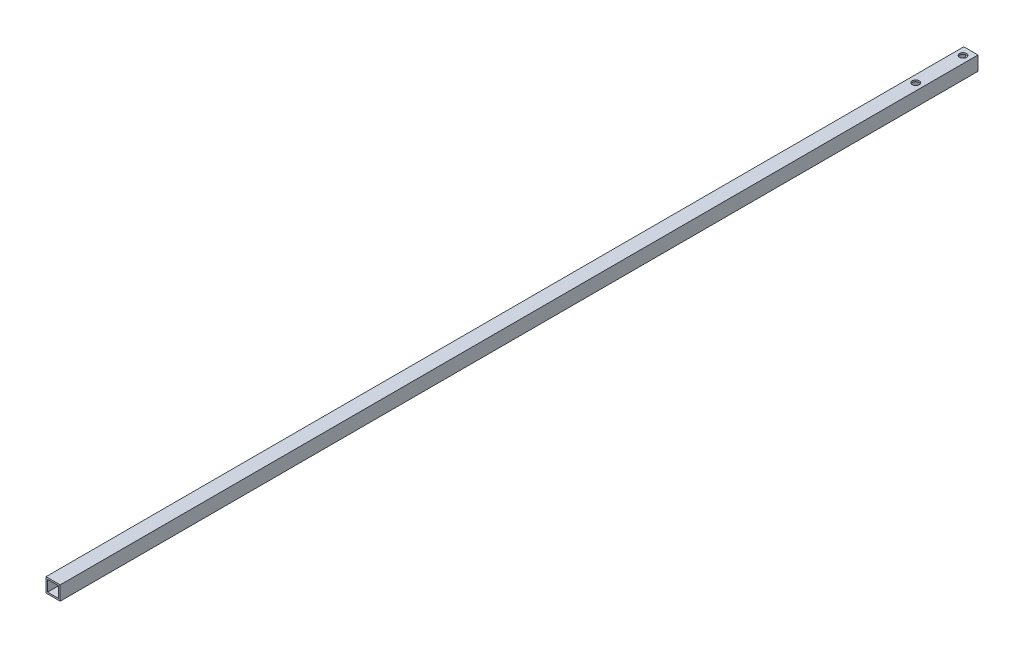
SolidWorks part; units mm, degrees
ref_plane "正面" through (0, 0, 0) normal (0, 0, 1) x (1, 0, 0)
ref_plane "平面" through (0, 0, 0) normal (0, 1, 0) x (1, 0, 0)
ref_plane "右側面" through (0, 0, 0) normal (1, 0, 0) x (0, 0, -1)
sketch "ｽｹｯﾁ1" plane through (0, 0, 0) normal (0, 0, 1) x (1, 0, 0)
  line L1 (-4.5, 4.5) -> (4.5, 4.5)
  line L2 (-4.5, 4.5) -> (-4.5, -4.5)
  line L3 (-4.5, -4.5) -> (4.5, -4.5)
  line L4 (4.5, 4.5) -> (4.5, -4.5)
  line L5 (-4.5, 4.5) -> (4.5, -4.5) construction
  line L6 (-4.5, -4.5) -> (4.5, 4.5) construction
  point P0 (0, 0)
  dimension "D1" = 9
  dimension "D2" = 9
extrude "ﾎﾞｽ - 押し出し1" add sketch "ｽｹｯﾁ1" along normal blind 582
sketch "ｽｹｯﾁ2" plane through (0, 0, 582) normal (0, 0, 1) x (1, 0, 0)
  line L1 (-3.5, 3.5) -> (3.5, 3.5)
  line L2 (-3.5, 3.5) -> (-3.5, -3.5)
  line L3 (-3.5, -3.5) -> (3.5, -3.5)
  line L4 (3.5, 3.5) -> (3.5, -3.5)
  line L5 (-3.5, 3.5) -> (3.5, -3.5) construction
  line L6 (-3.5, -3.5) -> (3.5, 3.5) construction
  point P0 (0, 0)
  dimension "D1" = 7
  dimension "D2" = 7
extrude "ｶｯﾄ - 押し出し1" cut sketch "ｽｹｯﾁ2" against normal blind 582
sketch "ｽｹｯﾁ3" plane through (0, 4.5, 0) normal (0, 1, 0) x (1, 0, 0)
  line L0 (0, 0) -> (0, -5)
  line L1 (4.5, 0) -> (-4.5, 0) construction
  line L2 (0, -5) -> (0, -35)
  circle A0 centre (0, -5) radius 2.2
  circle A1 centre (0, -35) radius 2.2
  dimension "D3" = 4.4
  dimension "D4" = 4.4
  dimension "D1" = 5
  dimension "D2" = 30
extrude "ｶｯﾄ - 押し出し2" cut sketch "ｽｹｯﾁ3" against normal blind 582
sketch "ｽｹｯﾁ4" plane through (0, 4.5, 0) normal (0, 1, 0) x (1, 0, 0)
  line L0 (0.1602, -582) -> (0.1602, -572)
  line L1 (4.5, -582) -> (-4.5, -582) construction
  line L2 (0.1602, -572) -> (0.1602, -506)
  circle A0 centre (0.1602, -572) radius 2.2
  circle A1 centre (0.1602, -506) radius 2.2
  dimension "D3" = 4.4
  dimension "D4" = 4.4
  dimension "D1" = 10
  dimension "D2" = 66
